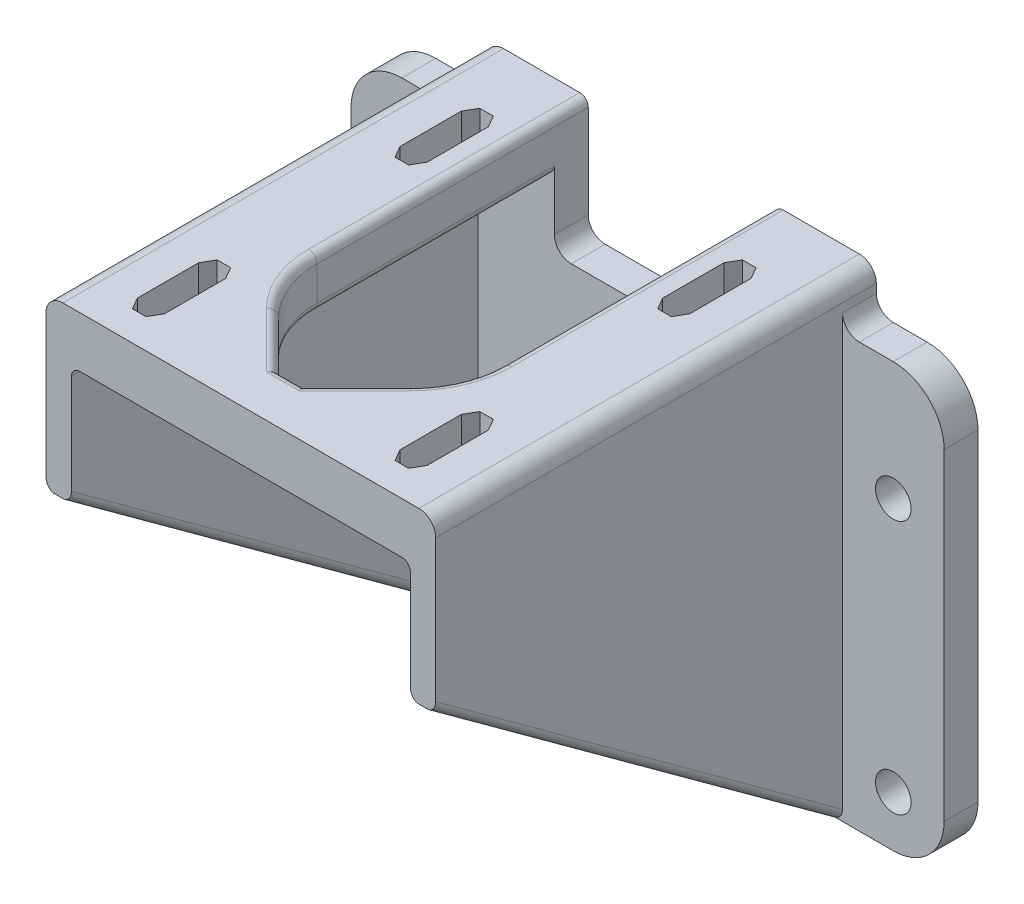
SolidWorks part; units mm, degrees
ref_plane "Front Plane" through (0, 0, 0) normal (0, 0, 1) x (1, 0, 0)
ref_plane "Top Plane" through (0, 0, 0) normal (0, 1, 0) x (1, 0, 0)
ref_plane "Right Plane" through (0, 0, 0) normal (1, 0, 0) x (0, 0, -1)
sketch "Sketch1" plane through (0, 0, 0) normal (0, 0, 1) x (1, 0, 0)
  line L1 (-35, -25) -> (35, -25)
  line L2 (-35, -25) -> (-35, 25)
  line L3 (-35, 25) -> (35, 25)
  line L4 (35, -25) -> (35, 25)
  line L5 (-35, -25) -> (35, 25) construction
  line L6 (-35, 25) -> (35, -25) construction
  point P0 (0, 0)
  dimension "D1" = 50
  dimension "D2" = 70
extrude "Boss-Extrude1" add sketch "Sketch1" along normal blind 4
sketch "Sketch2" plane through (0, 0, 0) normal (0, 0, 1) x (1, 0, 0)
  line L0 (-35, -25) -> (35, -25) construction
  line L1 (-23, -25) -> (-20, -25)
  line L2 (-23, -25) -> (-23, 30)
  line L4 (-20, -25) -> (-20, 24)
  line L5 (11, 24) -> (11, 30)
  line L6 (-20, 24) -> (-11, 24)
  line L7 (23, 30) -> (11, 30)
  line L9 (0, 0) -> (0, 12.9932) construction
  line L11 (-23, 30) -> (-11, 30)
  line L12 (-11, 24) -> (-11, 30)
  line L13 (20, 24) -> (11, 24)
  line L14 (20, -25) -> (20, 24)
  line L15 (23, -25) -> (23, 30)
  line L16 (23, -25) -> (20, -25)
  dimension "D1" = 3
  dimension "D3" = 12
  dimension "D4" = 46
  dimension "D2" = 6
  dimension "D5" = 30
extrude "Boss-Extrude2" add sketch "Sketch2" along normal blind 52
sketch "Sketch3" plane through (0, 0, 0) normal (-1, 0, 0) x (0, 0, 1)
  line L0 (52, 10) -> (4, -25)
  line L2 (4, -25) -> (0, -25) construction
  line L4 (52, 30) -> (52, -25) construction
  line L5 (4, 25) -> (4, -25) construction
  dimension "D1" = 20
extrude "Cut-Extrude3" cut sketch "Sketch3" against normal through all and the other way through all
fillet "Fillet1" radius 6 4 edges at (35, 25, 2) (-35, 25, 2) (35, -25, 2) (-35, -25, 2)
sketch "Sketch6" plane through (0, 30, 0) normal (0, 1, 0) x (1, 0, 0)
  line L0 (-38.1578, -28) -> (38.1578, -28) construction
  line L2 (-17.1, -47.1144) -> (-17.1, -39.8856)
  line L3 (-17.1, -39.8856) -> (-16.3, -38.5)
  line L4 (-16.3, -38.5) -> (-14.7, -38.5)
  line L5 (0, 0) -> (0, -28) construction
  line L6 (-14.7, -38.5) -> (-13.9, -39.8856)
  line L7 (-13.9, -39.8856) -> (-13.9, -47.1144)
  line L8 (-13.9, -47.1144) -> (-14.7, -48.5)
  line L9 (-14.7, -48.5) -> (-16.3, -48.5)
  line L10 (-16.3, -48.5) -> (-17.1, -47.1144)
  line L11 (-15.5, -38.5) -> (-15.5, -48.5) construction
  line L12 (-17.1, -43.5) -> (-13.9, -43.5) construction
  line L13 (16.3, -48.5) -> (17.1, -47.1144)
  line L14 (14.7, -48.5) -> (16.3, -48.5)
  line L15 (13.9, -47.1144) -> (14.7, -48.5)
  line L16 (13.9, -39.8856) -> (13.9, -47.1144)
  line L17 (14.7, -38.5) -> (13.9, -39.8856)
  line L18 (16.3, -38.5) -> (14.7, -38.5)
  line L19 (17.1, -39.8856) -> (16.3, -38.5)
  line L20 (17.1, -47.1144) -> (17.1, -39.8856)
  line L21 (17.1, -8.8856) -> (17.1, -16.1144)
  line L22 (17.1, -16.1144) -> (16.3, -17.5)
  line L23 (16.3, -17.5) -> (14.7, -17.5)
  line L24 (14.7, -17.5) -> (13.9, -16.1144)
  line L25 (13.9, -16.1144) -> (13.9, -8.8856)
  line L26 (13.9, -8.8856) -> (14.7, -7.5)
  line L27 (14.7, -7.5) -> (16.3, -7.5)
  line L28 (16.3, -7.5) -> (17.1, -8.8856)
  line L29 (-16.3, -7.5) -> (-17.1, -8.8856)
  line L30 (-14.7, -7.5) -> (-16.3, -7.5)
  line L31 (-13.9, -8.8856) -> (-14.7, -7.5)
  line L32 (-13.9, -16.1144) -> (-13.9, -8.8856)
  line L33 (-14.7, -17.5) -> (-13.9, -16.1144)
  line L34 (-16.3, -17.5) -> (-14.7, -17.5)
  line L35 (-17.1, -16.1144) -> (-16.3, -17.5)
  line L36 (-17.1, -8.8856) -> (-17.1, -16.1144)
  dimension "D4" = 10
  dimension "D2" = 30
  dimension "D3" = 3.2
  dimension "D5" = 31
  dimension "D1" = 28
  dimension "D6" = 31
extrude "Cut-Extrude6" cut sketch "Sketch6" against normal through all contours L29 L36 L35 L34 L33 L32 L31 L30 | L10 L9 L8 L7 L6 L4 L3 L2
sketch "Sketch7" plane through (0, 0, 4) normal (0, 0, 1) x (1, 0, 0)
  line L1 (-11, 25) -> (11, 25)
  line L2 (-11, 25) -> (-11, 16)
  line L3 (-11, 16) -> (11, 16)
  line L4 (11, 25) -> (11, 16)
  line L5 (0, 0) -> (0, 28.0703) construction
  line L7 (-11, 24) -> (-11, 30) construction
  line L8 (11, 25) -> (-11, 25) construction
  dimension "D2" = 9
extrude "Cut-Extrude7" cut sketch "Sketch7" against normal through all
hole_wizard "Ø4.2 (4.2) Diameter Hole1" positions "Sketch9" profile "Sketch8" hole size "Ø4.2" standard "ANSI Metric"
sketch "Sketch9" plane through (0, 0, 4) normal (0, 0, 1) x (1, 0, 0)
  line L0 (0, -25) -> (0, -3.4871) construction
  line L1 (-29, -25) -> (-23, -25) construction
  line L2 (-35, 19) -> (-35, -19) construction
  line L3 (-29, -25) -> (29, -25) construction
  point P8 (-29, -19)
  point P10 (-29, 11)
  point P17 (29, -19)
  point P18 (29, 11)
  dimension "D1" = 30
  dimension "D2" = 6
  dimension "D3" = 6
sketch "Sketch8" plane through (-29, -19, 4) normal (1, 0, 0) x (0, -1, 0)
  line L0 (0, 0) -> (0, 5.2618)
  line L1 (0, 5.2618) -> (2.1, 4)
  line L2 (2.1, 4) -> (2.1, 0)
  line L5 (2.1, 0) -> (0, 0)
  line L10 (0, 5.2618) -> (-2.1, 4) construction
  line L11 (0, -6.35) -> (0, 107.95) construction
  dimension "Hole Dia." = 4.2
  dimension "Hole Depth" = 4
  dimension "Drill Angle" = 118
sketch "Sketch10" plane through (0, 0, 4) normal (0, 0, 1) x (1, 0, 0)
  line L0 (1.4142, 5.8995) -> (9.8995, -2.5858)
  line L1 (-1.4142, 5.8995) -> (-9.8995, -2.5858)
  line L2 (9.8995, -5.4142) -> (1.4142, -13.8995)
  line L3 (-9.8995, -5.4142) -> (-1.4142, -13.8995)
  line L4 (-11.3137, -4) -> (11.3137, -4) construction
  line L5 (0, 7.3137) -> (0, -15.3137) construction
  line L6 (-20, -25) -> (20, -25) construction
  arc A0 (1.4142, -13.8995) -> (-1.4142, -13.8995) centre (0, -12.4853) cw
  arc A1 (-9.8995, -2.5858) -> (-9.8995, -5.4142) centre (-8.4853, -4) ccw
  arc A2 (-1.4142, 5.8995) -> (1.4142, 5.8995) centre (0, 4.4853) cw
  arc A3 (9.8995, -2.5858) -> (9.8995, -5.4142) centre (8.4853, -4) cw
  dimension "D3" = 2
  dimension "D1" = 16
  dimension "D2" = 21
extrude "Cut-Extrude8" cut sketch "Sketch10" against normal up to next
sketch "Sketch11" plane through (0, 30, 0) normal (0, 1, 0) x (1, 0, 0)
  line L0 (-1.5, -46.0563) -> (-7.7782, -39.7782)
  line L1 (-11, -52) -> (-11, 0) construction
  line L2 (-11, -32) -> (-11, -52)
  line L3 (-11, -52) -> (11, -52)
  line L4 (0, 0) -> (0, -52) construction
  line L5 (11, -32) -> (11, -52)
  line L6 (1.5, -46.0563) -> (7.7782, -39.7782)
  line L7 (-11, -32) -> (11, -32) construction
  line L10 (-1.5, -46.0563) -> (1.5, -46.0563)
  arc A0 (-7.7782, -39.7782) -> (-11, -32) centre (0, -32) cw
  arc A1 (7.7782, -39.7782) -> (11, -32) centre (0, -32) ccw
  dimension "D1" = 32
  dimension "D2" = 3
extrude "Boss-Extrude3" add sketch "Sketch11" against normal up to surface (6 mm away) up to face at (-15.5, 24, 28)
fillet "Fillet2" radius 2 6 edges at (-23, 30, 26) (23, 30, 26) (23, 25, 2) (11, 16, 2) (-11, 16, 2) (-23, 25, 2)
fillet "Fillet3" radius 1 7 edges at (11, 30, 16) (-11, 30, 16) (4.6391, 30, 42.9173) (10.1627, 30, 36.2095) (-4.6391, 30, 42.9173) (-10.1627, 30, 36.2095) (0, 30, 46.0563)
fillet "Fillet4" radius 1 13 edges at (-23, -7.5, 28) (-20, -7.5, 28) (23, -7.5, 28) (20, -7.5, 28) (20, 24, 28) (-20, 24, 28) (11, 24, 18) (-11, 24, 18) (4.6391, 24, 42.9173) (10.1627, 24, 36.2095) (-4.6391, 24, 42.9173) (-10.1627, 24, 36.2095) (0, 24, 46.0563)
